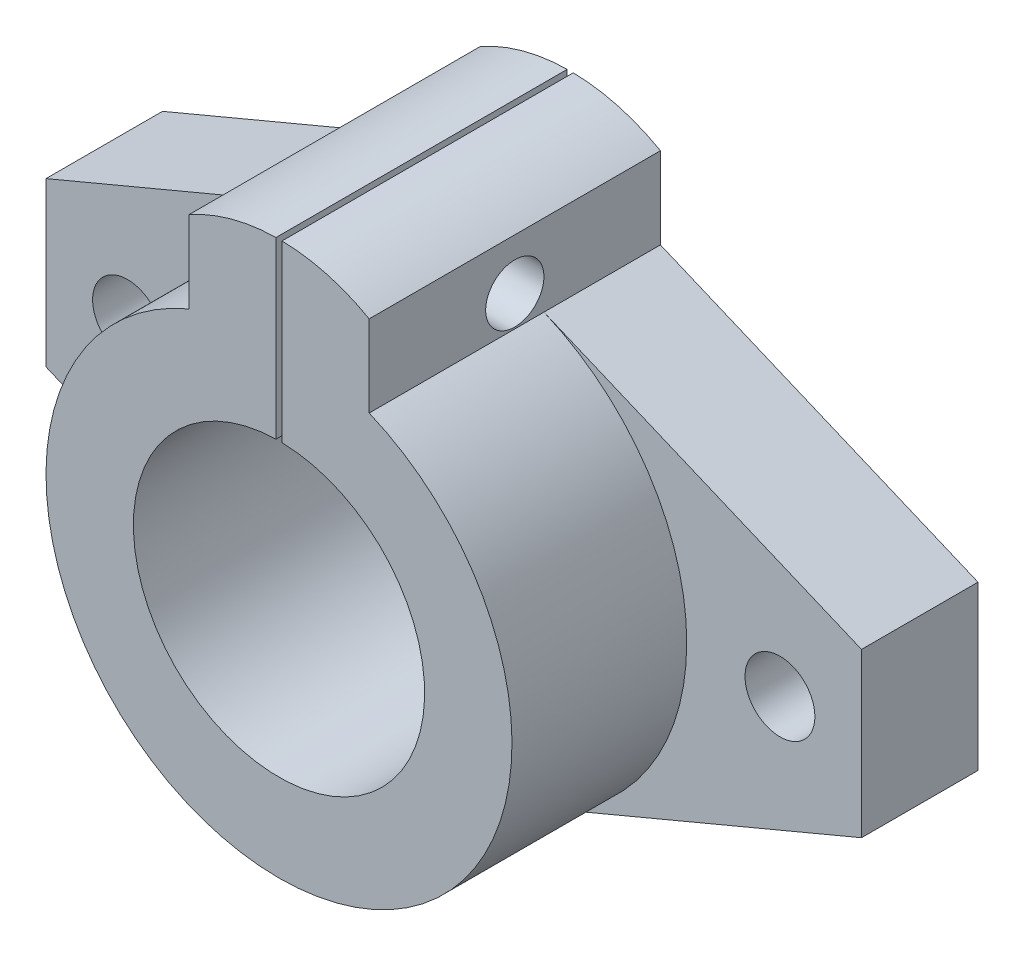
SolidWorks part; units mm, degrees
ref_plane "前视基准面" through (0, 0, 0) normal (0, 0, 1) x (1, 0, 0)
ref_plane "上视基准面" through (0, 0, 0) normal (0, 1, 0) x (1, 0, 0)
ref_plane "右视基准面" through (0, 0, 0) normal (1, 0, 0) x (0, 0, -1)
sketch "草图1" plane through (0, 0, 0) normal (0, 0, 1) x (1, 0, 0)
  line L0 (-7.7403, 18.4415) -> (-7.7403, 25.4415)
  line L1 (-35, -7) -> (-35, 7)
  line L2 (-35, 7) -> (-7.7403, 18.4415)
  line L3 (-35, -7) -> (-7.7403, -18.4415)
  line L4 (7.7403, 18.4415) -> (7.7403, 25.4415)
  line L5 (35, -7) -> (7.7403, -18.4415)
  line L6 (35, -7) -> (35, 7)
  line L7 (35, 7) -> (7.7403, 18.4415)
  line L8 (0, 0) -> (-28, 0) construction
  circle A0 centre (0, 0) radius 12.5
  arc A1 (-7.7403, 18.4415) -> (7.7403, 18.4415) centre (0, 0) ccw
  arc A2 (-7.7403, 25.4415) -> (7.7403, 25.4415) centre (0, 11.8749) cw
  circle A3 centre (-28, 0) radius 3
  circle A4 centre (28, 0) radius 3
  dimension "D1" = 28
  dimension "D3" = 25
  dimension "D4" = 20
  dimension "D5" = 6
  dimension "D2" = 28
extrude "凸台-拉伸2" add sketch "草图1" along normal blind 10 contours A1 L5 L6 L7 | A2 L0 A1 L4 A0 | A1 L2 L1 L3
sketch "草图2" plane through (0, 0, 10) normal (0, 0, 1) x (1, 0, 0)
  line L0 (-7.7403, 18.4415) -> (-7.7403, 25.4415)
  line L1 (7.7403, 18.4415) -> (7.7403, 25.4415)
  circle A0 centre (0, 0) radius 12.5
  arc A1 (-7.7403, 18.4415) -> (7.7403, 18.4415) centre (0, 0) ccw
  arc A2 (-7.7403, 25.4415) -> (7.7403, 25.4415) centre (0, 11.8749) cw
extrude "凸台-拉伸3" add sketch "草图2" along normal blind 15
sketch "草图3" plane through (0, 0, 25) normal (0, 0, 1) x (1, 0, 0)
  line L1 (-0.2586, 12.3781) -> (-0.2586, 31.1043)
  line L2 (0.2586, 12.3781) -> (0.2586, 31.1043)
  line L3 (-0.2586, 12.3781) -> (0.2586, 12.3781)
  line L4 (-0.2586, 31.1043) -> (0.2586, 31.1043)
extrude "切除-拉伸1" cut sketch "草图3" against normal through all
sketch "草图4" plane through (7.7403, 0, 0) normal (1, 0, 0) x (0, 0, -1)
  circle A0 centre (-12.5, 21.0864) radius 2.5
extrude "切除-拉伸2" cut sketch "草图4" against normal through all
